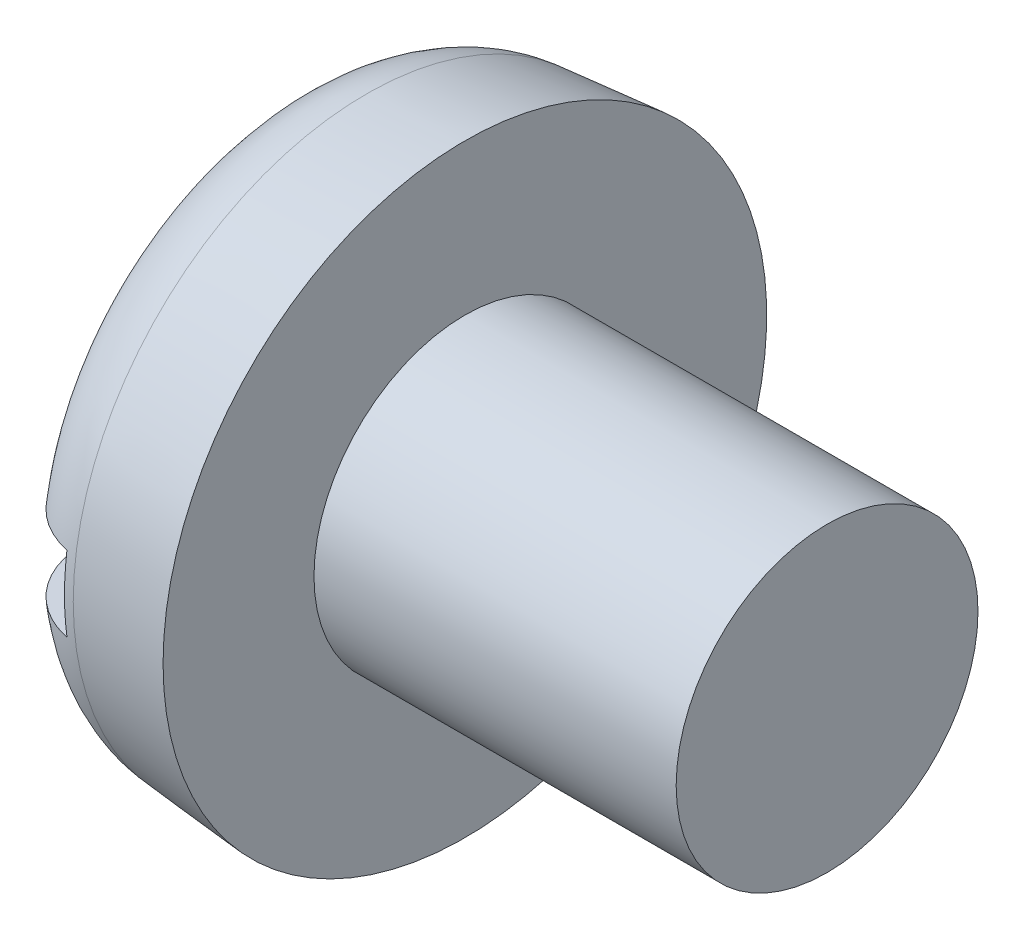
SolidWorks part; units mm, degrees
ref_plane "Plane1" through (0, 0, 0) normal (0, 0, 1) x (1, 0, 0)
ref_plane "Plane2" through (0, 0, 0) normal (0, 1, 0) x (1, 0, 0)
ref_plane "Plane3" through (0, 0, 0) normal (1, 0, 0) x (0, 0, -1)
sketch "BodySke" plane through (0, 0, 0) normal (0, 0, 1) x (1, 0, 0)
  line L0 (6, 5) -> (6, 10)
  line L1 (0, 0) -> (0, 9.4751)
  line L2 (-25.4, 0) -> (127, 0) construction
  line L3 (18, 0) -> (0, 0)
  line L4 (6, 5) -> (18, 5)
  line L5 (18, 5) -> (18, 0)
  line L6 (0, 9.4751) -> (6, 10)
  line L9 (7.5, 6.5875) -> (7.5, -2.9375) construction
  line L10 (6, 6.35) -> (6, -3.175) construction
  dimension "Head_ht" = 6
  dimension "Diameter" = 10
  dimension "Length" = 12
  dimension "Head_dia" = 20
  dimension "Advance" = 1.5
  dimension "Thread_nom" = 12
  dimension "Head_side_angle" = 5
revolve "Base-Revolve" add sketch "BodySke"
cosmetic thread "ThreadCosmetic"
fillet "Fillet1" [suppressed] radius 0.4
fillet "Fillet2" radius 3 1 edges at (0, 0, 9.4751)
sketch "Sketch2" plane through (0, 0, 0) normal (1, 0, 0) x (0, 0, -1)
  line L0 (10, -1.25) -> (-10, -1.25)
  line L1 (10, -1.25) -> (10, 1.25)
  line L2 (-10, 1.25) -> (10, 1.25)
  line L3 (-10, 1.25) -> (-10, -1.25)
  dimension "D1" = 20
  dimension "D2" = 10
  dimension "Slot_width" = 2.5
  dimension "D3" = 1.25
extrude "Slot" cut sketch "Sketch2" along normal blind 2.4
sketch "ThdSchSke" plane through (0, 0, 0) normal (0, 0, 1) x (1, 0, 0)
  line L0 (9, -4.172) -> (8.4202, -5)
  line L1 (9, -4.172) -> (9.5798, -5)
  line L2 (9.5798, -5) -> (9.5798, -6.25)
  line L3 (-3.175, 0) -> (5.1513, 0) construction
  line L5 (9.5798, -6.25) -> (8.4202, -6.25)
  line L6 (8.4202, -6.25) -> (8.4202, -5)
  dimension "Thread_minor" = 8.344
  dimension "Diameter" = 10
  dimension "Start" = 9
  dimension "SideAngle" = 55
  dimension "VeeAngle" = 70
  dimension "Overcut" = 12.5
revolve "ThreadSchematic" [suppressed] cut sketch "ThdSchSke" angle 360 about L3
pattern_linear "ThdSchPat" [suppressed]
equation "\"D1@Sketch2\" = \"Head_dia@BodySke\""
equation "\"D2@Sketch2\" = \"D1@Sketch2\" / 2"
equation "\"D3@Sketch2\" = \"Slot_width@Sketch2\" / 2"
equation "\"Thread_length@ThreadCosmetic\" = ((sgn( (\"Length@BodySke\" - \"Advance@BodySke\" * 2.0 ) - \"Thread_nom@BodySke\" )-1)*( (\"Length@BodySke\" - \"Advance@BodySke\"  * 2.0) - \"Thread_nom@BodySke\" ))/-2+ \"Thread_nom@BodySke\""
equation "\"Thread_minor@ThdSchSke\" = \"Thread_minor@ThreadCosmetic\""
equation "\"Diameter@ThdSchSke\" = \"Diameter@BodySke\""
equation "\"Overcut@ThdSchSke\" = \"Diameter@BodySke\" * 1.25"
equation "\"Start@ThdSchSke\" = \"Head_ht@BodySke\" + \"Length@BodySke\" - \"Thread_length@ThreadCosmetic\"  '---Non-countersunk---"
equation "\"Num_threads@ThdSchPat\" = int( \"Thread_length@ThreadCosmetic\" / \"Advance@BodySke\" + 0.999 )  + 1"
equation "\"Advance@ThdSchPat\" = \"Thread_length@ThreadCosmetic\" /  (\"Num_threads@ThdSchPat\" - 1) 'relax it"
